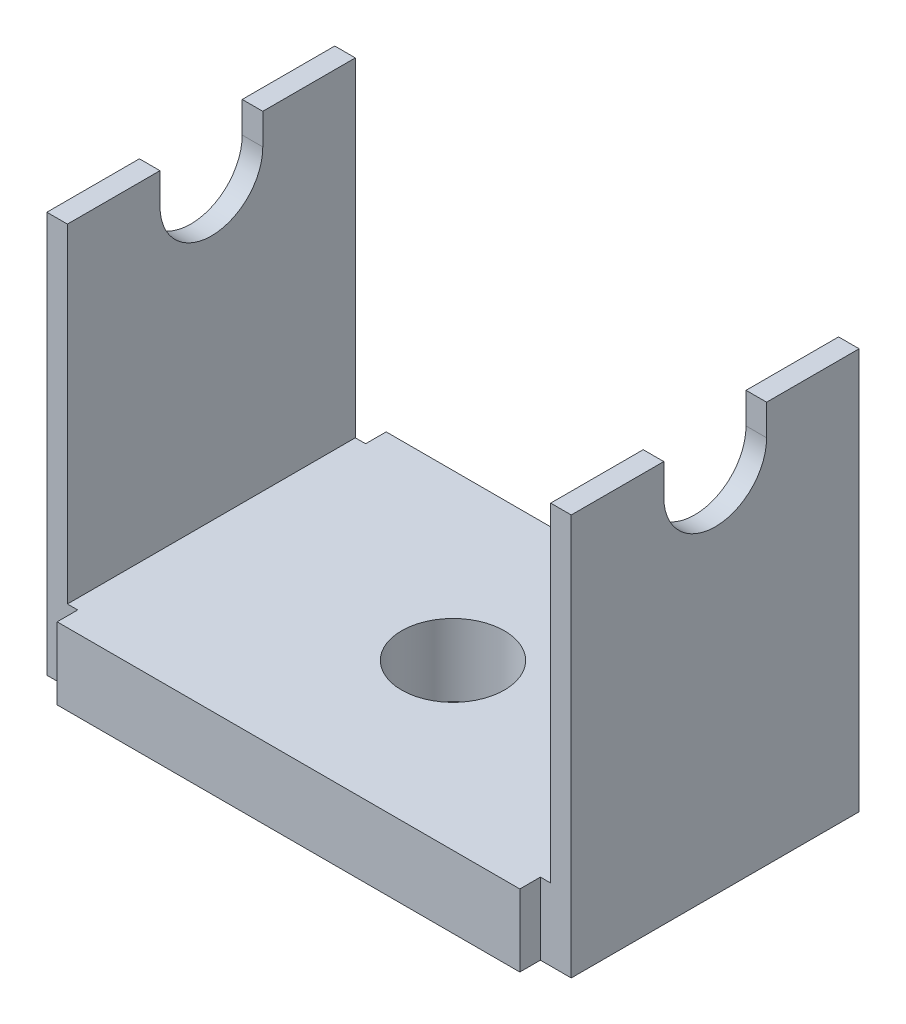
SolidWorks part; units mm, degrees
ref_plane "Front Plane" through (0, 0, 0) normal (0, 0, 1) x (1, 0, 0)
ref_plane "Top Plane" through (0, 0, 0) normal (0, 1, 0) x (1, 0, 0)
ref_plane "Right Plane" through (0, 0, 0) normal (1, 0, 0) x (0, 0, -1)
sketch "Sketch1" plane through (0, 0, 0) normal (0, 0, 1) x (1, 0, 0)
  line L0 (-25.5, 3) -> (-25.5, -36)
  line L1 (-25.5, -36) -> (25.5, -36)
  line L2 (25.5, -36) -> (25.5, 3)
  line L3 (25.5, 3) -> (23.5, 3)
  line L4 (23.5, 3) -> (23.5, -29)
  line L5 (23.5, -29) -> (-23.5, -29)
  line L6 (-23.5, -29) -> (-23.5, 3)
  line L7 (-23.5, 3) -> (-25.5, 3)
  dimension "D1" = 3
  dimension "D2" = 51
  dimension "D3" = 2
  dimension "D4" = 39
  dimension "D5" = 7
  dimension "D6" = 23.5
extrude "Boss-Extrude1" add sketch "Sketch1" against normal mid plane 28
sketch "Sketch2" plane through (0, 0, 0) normal (1, 0, 0) x (0, 0, -1)
  line L0 (-14, -36) -> (-16, -36)
  line L1 (14, -36) -> (-14, -36) construction
  line L2 (-16, -36) -> (-16, -29)
  line L3 (-16, -29) -> (-13, -29)
  line L4 (-13, -29) -> (-13, -33)
  line L5 (-13, -33) -> (-14, -33)
  line L6 (-14, -33) -> (-14, -36)
  dimension "D1" = 3
  dimension "D2" = 1
  dimension "D3" = 7
extrude "Boss-Extrude2" add sketch "Sketch2" along normal mid plane 45
mirror "Mirror1" about plane through (0, 0, 0) normal (0, 0, 1) of "Boss-Extrude2"
sketch "Sketch3" plane through (25.5, 0, 0) normal (1, 0, 0) x (0, 0, -1)
  line L0 (14, -36) -> (-14, -36) construction
  line L1 (-5, 0) -> (-5, 3)
  line L2 (14, 3) -> (-14, 3) construction
  line L3 (5, 0) -> (5, 3)
  line L4 (0, -36) -> (0, 0) construction
  line L5 (-5, 3) -> (5, 3)
  arc A0 (-5, 0) -> (5, 0) centre (0, 0) ccw
  dimension "D1" = 10
  dimension "D2" = 36
extrude "Cut-Extrude1" cut sketch "Sketch3" against normal through all
sketch "Sketch4" plane through (0, -29, 0) normal (0, 1, 0) x (1, 0, 0)
  line L0 (0, 0) -> (-23.5, 0) construction
  line L1 (-23.5, -5) -> (-23.5, 5) construction
  line L2 (-23.5, 14) -> (-23.5, -14) construction
  circle A0 centre (0, 0) radius 5
  dimension "D1" = 10
extrude "Cut-Extrude2" cut sketch "Sketch4" against normal through all
equation "\"D1@Sketch1\" = 39-36"
